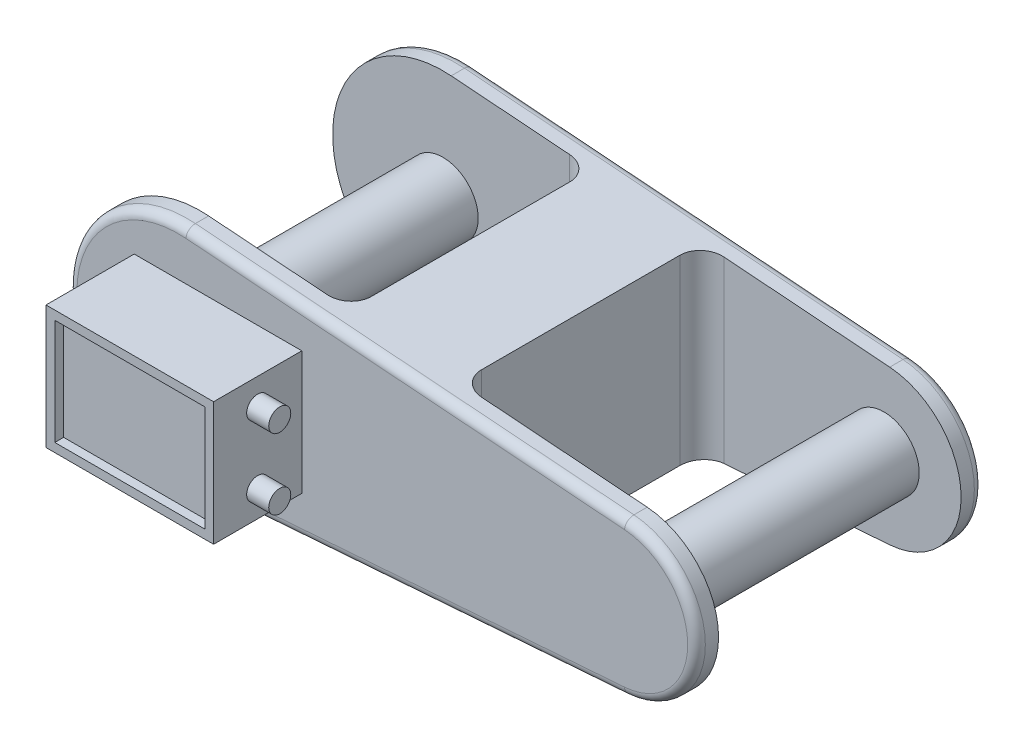
SolidWorks part; units mm, degrees
ref_plane "Ön Düzlem" through (0, 0, 0) normal (0, 0, 1) x (1, 0, 0)
ref_plane "Üst Düzlem" through (0, 0, 0) normal (0, 1, 0) x (1, 0, 0)
ref_plane "Sağ Düzlem" through (0, 0, 0) normal (1, 0, 0) x (0, 0, -1)
sketch "Çizim1" plane through (0, 0, 0) normal (0, 0, 1) x (1, 0, 0)
  line L0 (1.875, 24.9296) -> (101.3125, 17.4507)
  line L1 (1.875, -24.9296) -> (101.3125, -17.4507)
  arc A0 (1.875, 24.9296) -> (1.875, -24.9296) centre (0, 0) ccw
  arc A1 (101.3125, -17.4507) -> (101.3125, 17.4507) centre (100, 0) ccw
  dimension "D1" = 50
  dimension "D2" = 35
  dimension "D3" = 100
extrude "Yükseklik-Ekstrüzyon1" add sketch "Çizim1" along normal mid plane 65
sketch "Çizim3" plane through (0, 0, 0) normal (0, 1, 0) x (1, 0, 0)
  line L0 (-25, 32.5) -> (-25, -32.5) construction
  line L1 (33.75, -27.5) -> (-25, -27.5)
  line L2 (33.75, -27.5) -> (33.75, 27.5)
  line L3 (33.75, 27.5) -> (-25, 27.5)
  line L4 (-25, -27.5) -> (-25, 27.5)
  line L5 (33.75, -27.5) -> (-25, 27.5) construction
  line L6 (33.75, 27.5) -> (-25, -27.5) construction
  line L8 (117.5, -32.5) -> (117.5, 32.5) construction
  line L9 (58.75, -27.5) -> (117.5, -27.5)
  line L10 (58.75, -27.5) -> (58.75, 27.5)
  line L11 (58.75, 27.5) -> (117.5, 27.5)
  line L12 (117.5, -27.5) -> (117.5, 27.5)
  line L13 (58.75, -27.5) -> (117.5, 27.5) construction
  line L14 (58.75, 27.5) -> (117.5, -27.5) construction
  point P0 (4.375, 0)
  point P11 (88.125, 0)
  dimension "D1" = 55
  dimension "D2" = 55
  dimension "D3" = 25
extrude "Kes-Ekstrüzyon1" cut sketch "Çizim3" against normal through all both and the other way through all
sketch "Çizim4" plane through (0, 0, 0) normal (0, 0, 1) x (1, 0, 0)
  circle A0 centre (0, 0) radius 8
  circle A1 centre (100, 0) radius 8
  dimension "D1" = 16
extrude "Yükseklik-Ekstrüzyon2" add sketch "Çizim4" along normal mid plane 65
fillet "Radyus1" radius 5 4 edges at (33.75, 0, -27.5) (33.75, 0, 27.5) (58.75, 0, 27.5) (58.75, 0, -27.5)
sketch "Çizim5" plane through (0, 0, 32.5) normal (0, 0, 1) x (1, 0, 0)
  line L1 (-10, -14) -> (28, -14)
  line L2 (-10, -14) -> (-10, 14)
  line L3 (-10, 14) -> (28, 14)
  line L4 (28, -14) -> (28, 14)
  line L5 (-10, -14) -> (28, 14) construction
  line L6 (-10, 14) -> (28, -14) construction
  point P0 (9, 0)
  dimension "D1" = 28
  dimension "D2" = 38
  dimension "D3" = 10
extrude "Yükseklik-Ekstrüzyon3" add sketch "Çizim5" along normal blind 20 separate body
sketch "Çizim6" plane through (28, 0, 0) normal (1, 0, 0) x (0, 0, -1)
  line L0 (-52.5, 14) -> (-32.5, 14) construction
  line L1 (-52.5, -14) -> (-32.5, -14) construction
  circle A0 centre (-42.5, 8) radius 2.5
  circle A1 centre (-42.5, -8) radius 2.5
  point P6 (-42.5, 14)
  dimension "D1" = 5
  dimension "D2" = 6
  dimension "D3" = 6
extrude "Yükseklik-Ekstrüzyon4" add sketch "Çizim6" along normal blind 5
sketch "Çizim7" plane through (0, 0, 52.5) normal (0, 0, 1) x (1, 0, 0)
  line L12 (26, -12) -> (26, 12)
  line L13 (26, 12) -> (-8, 12)
  line L14 (-8, 12) -> (-8, -12)
  line L15 (-8, -12) -> (26, -12)
  line L16 (26, -12) -> (26, 12)
  line L17 (26, 12) -> (-8, 12)
  line L18 (-8, 12) -> (-8, -12)
  line L19 (-8, -12) -> (26, -12)
  dimension "D1" = 2
extrude "Kes-Ekstrüzyon2" cut sketch "Çizim7" against normal blind 2
fillet "Radyus2" radius 2 8 edges at (117.5, 0, -32.5) (51.5938, -21.1902, -32.5) (-25, 0, -32.5) (51.5938, 21.1902, 32.5) (117.5, 0, 32.5) (51.5938, -21.1902, 32.5) (51.5938, 21.1902, -32.5) (-25, 0, 32.5)
